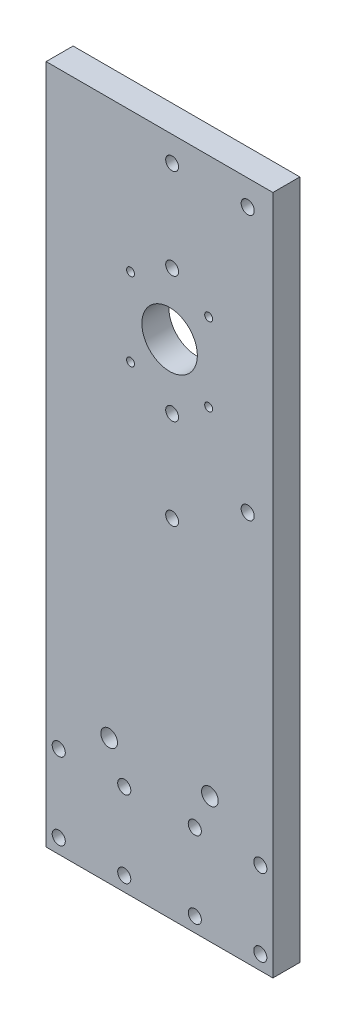
SolidWorks part; units mm, degrees
ref_plane "Plano frontal" through (0, 0, 0) normal (0, 0, 1) x (1, 0, 0)
ref_plane "Plano superior" through (0, 0, 0) normal (0, 1, 0) x (1, 0, 0)
ref_plane "Plano direito" through (0, 0, 0) normal (1, 0, 0) x (0, 0, -1)
sketch "Esboço1" plane through (0, 0, 0) normal (0, 0, 1) x (1, 0, 0)
  line L1 (45, -135) -> (-45, -135)
  line L2 (45, -135) -> (45, 135)
  line L3 (45, 135) -> (-45, 135)
  line L4 (-45, -135) -> (-45, 135)
  line L5 (45, -135) -> (-45, 135) construction
  line L6 (45, 135) -> (-45, -135) construction
  point P0 (0, 0)
  dimension "D1" = 270
  dimension "D2" = 90
extrude "Ressalto-extrusão1" add sketch "Esboço1" along normal blind 10.7
hole_wizard "Furo roscado para conduíte de M5x0.81" positions "Esboço6" profile "Esboço7" tap size "M5x0.8" standard "Helicoil® Metric" end condition through all
sketch "Esboço6" plane through (0, 0, 0) normal (0, 0, -1) x (-1, 0, 0)
  line L0 (-45, -135) -> (-45, 135) construction
  line L1 (45, -135) -> (-45, -135) construction
  line L2 (0, -143.319) -> (0, -76.6051) construction
  point P0 (-40, -98.75)
  point P2 (-14, -98.75)
  point P4 (-40, -129.25)
  point P6 (-14, -129.25)
  point P22 (14, -129.25)
  point P23 (40, -129.25)
  point P24 (14, -98.75)
  point P25 (40, -98.75)
  dimension "D1" = 5
  dimension "D2" = 26
  dimension "D3" = 5.75
  dimension "D4" = 30.5
sketch "Esboço7" plane through (40, -98.75, 0) normal (1, 0, 0) x (0, 1, 0)
  line L0 (0, 0) -> (0, 10.7)
  line L1 (0, 10.7) -> (2.6, 10.7)
  line L2 (2.6, 10.7) -> (2.6, 0)
  line L5 (2.6, 0) -> (0, 0)
  line L11 (0, -6.35) -> (0, 107.95) construction
  dimension "Thru Tap Drill Dia." = 5.2
  dimension "Thru Tap Drill Depth" = 10.7
cosmetic thread "Rosca de furo1"
cosmetic thread "Rosca de furo2"
cosmetic thread "Rosca de furo3"
cosmetic thread "Rosca de furo4"
cosmetic thread "Rosca de furo5"
cosmetic thread "Rosca de furo6"
cosmetic thread "Rosca de furo7"
cosmetic thread "Rosca de furo8"
hole_wizard "Furo roscado para conduíte de 1/4-281" positions "Esboço8" profile "Esboço9" tap size "1/4-28" standard "Helicoil® Inch" end condition through all
sketch "Esboço8" plane through (0, 0, 0) normal (0, 0, -1) x (-1, 0, 0)
  line L0 (-45, -135) -> (-45, 135) construction
  line L1 (0, -142.4879) -> (0, -53.1789) construction
  circle A0 centre (-40, -98.75) radius 2.6 construction
  point P0 (-20, -85)
  point P13 (20, -85)
  dimension "D1" = 25
  dimension "D2" = 13.75
sketch "Esboço9" plane through (20, -85, 0) normal (1, 0, 0) x (0, 1, 0)
  line L0 (0, 0) -> (0, 10.7)
  line L1 (0, 10.7) -> (3.3147, 10.7)
  line L2 (3.3147, 10.7) -> (3.3147, 0)
  line L5 (3.3147, 0) -> (0, 0)
  line L11 (0, -6.35) -> (0, 107.95) construction
  dimension "Thru Tap Drill Dia." = 6.6294
  dimension "Thru Tap Drill Depth" = 10.7
cosmetic thread "Rosca de furo9"
cosmetic thread "Rosca de furo10"
hole_wizard "Furo roscado para conduíte de M5x0.82" positions "Esboço10" profile "Esboço11" tap size "M5x0.8" standard "Helicoil® Metric" end condition through all
sketch "Esboço10" plane through (0, 0, 0) normal (0, 0, -1) x (-1, 0, 0)
  line L0 (-45, 135) -> (45, 135) construction
  line L1 (-45, -135) -> (-45, 135) construction
  point P0 (-35, 125)
  point P2 (-35, 20)
  dimension "D1" = 10
  dimension "D2" = 10
  dimension "D3" = 105
sketch "Esboço11" plane through (35, 125, 0) normal (1, 0, 0) x (0, 1, 0)
  line L0 (0, 0) -> (0, 10.7)
  line L1 (0, 10.7) -> (2.6, 10.7)
  line L2 (2.6, 10.7) -> (2.6, 0)
  line L5 (2.6, 0) -> (0, 0)
  line L11 (0, -6.35) -> (0, 107.95) construction
  dimension "Thru Tap Drill Dia." = 5.2
  dimension "Thru Tap Drill Depth" = 10.7
cosmetic thread "Rosca de furo11"
cosmetic thread "Rosca de furo12"
hole_wizard "Furo roscado para conduíte de #10-321" positions "Esboço12" profile "Esboço13" tap size "#10-32" standard "Helicoil® Inch" end condition through all
sketch "Esboço12" plane through (0, 0, 0) normal (0, 0, -1) x (-1, 0, 0)
  line L0 (45, 135) -> (45, -135) construction
  line L1 (-45, 135) -> (45, 135) construction
  point P0 (-5, 125)
  point P2 (-5, 89)
  point P4 (-5, 39)
  point P6 (-5, 3)
  dimension "D1" = 50
  dimension "D2" = 10
  dimension "D3" = 36
  dimension "D4" = 50
  dimension "D5" = 36
sketch "Esboço13" plane through (5, 125, 0) normal (1, 0, 0) x (0, 1, 0)
  line L0 (0, 0) -> (0, 10.7)
  line L1 (0, 10.7) -> (2.5527, 10.7)
  line L2 (2.5527, 10.7) -> (2.5527, 0)
  line L5 (2.5527, 0) -> (0, 0)
  line L11 (0, -6.35) -> (0, 107.95) construction
  dimension "Thru Tap Drill Dia." = 5.1054
  dimension "Thru Tap Drill Depth" = 10.7
cosmetic thread "Rosca de furo13"
cosmetic thread "Rosca de furo14"
cosmetic thread "Rosca de furo15"
cosmetic thread "Rosca de furo16"
sketch "Esboço14" plane through (0, 0, 0) normal (0, 0, -1) x (-1, 0, 0)
  line L0 (45, 135) -> (45, -135) construction
  circle A0 centre (-4, 64) radius 11
  circle A1 centre (-5, 89) radius 2.5527 construction
  dimension "D1" = 22
  dimension "D3" = 25
  dimension "D2" = 49
extrude "Corte-extrusão1" cut sketch "Esboço14" against normal through all
hole_wizard "Furo roscado para conduíte de M3x0.51" positions "Esboço15" profile "Esboço16" tap size "M3x0.5" standard "Helicoil® Metric" end condition through all
sketch "Esboço15" plane through (0, 0, 0) normal (0, 0, -1) x (-1, 0, 0)
  line L0 (-26.4603, 64) -> (-4, 64) construction
  line L2 (-4, 79.5) -> (-4, 46.8564) construction
  circle A0 centre (-4, 64) radius 11 construction
  point P0 (-19.5, 79.5)
  point P14 (-19.5, 48.5)
  point P16 (11.5, 79.5)
  point P17 (11.5, 48.5)
  dimension "D1" = 15.5
  dimension "D2" = 15.5
sketch "Esboço16" plane through (19.5, 79.5, 0) normal (1, 0, 0) x (0, 1, 0)
  line L0 (0, 0) -> (0, 10.7)
  line L1 (0, 10.7) -> (1.575, 10.7)
  line L2 (1.575, 10.7) -> (1.575, 0)
  line L5 (1.575, 0) -> (0, 0)
  line L11 (0, -6.35) -> (0, 107.95) construction
  dimension "Thru Tap Drill Dia." = 3.15
  dimension "Thru Tap Drill Depth" = 10.7
cosmetic thread "Rosca de furo17"
cosmetic thread "Rosca de furo18"
cosmetic thread "Rosca de furo19"
cosmetic thread "Rosca de furo20"
